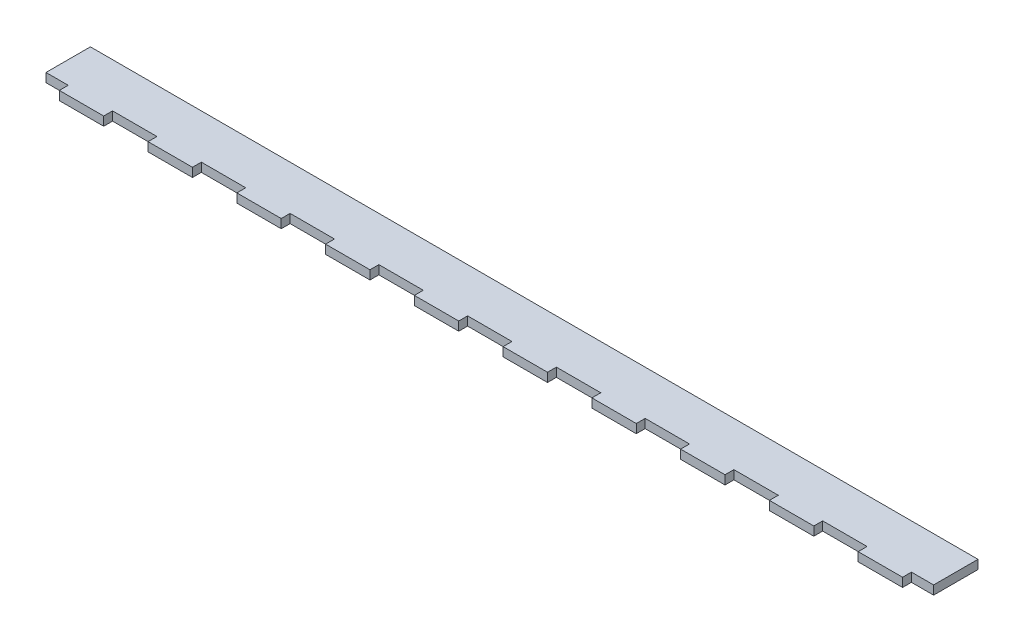
SolidWorks part; units mm, degrees
ref_plane "Front Plane" through (0, 0, 0) normal (0, 0, 1) x (1, 0, 0)
ref_plane "Top Plane" through (0, 0, 0) normal (0, 1, 0) x (1, 0, 0)
ref_plane "Right Plane" through (0, 0, 0) normal (1, 0, 0) x (0, 0, -1)
sketch "Sketch1" plane through (0, 0, 0) normal (0, 1, 0) x (1, 0, 0)
  line L0 (-190.5, -12.7) -> (-165.1, -12.7)
  line L1 (-254, 12.7) -> (254, 12.7)
  line L2 (-254, 12.7) -> (-254, -12.7)
  line L3 (-254, -12.7) -> (254, -12.7)
  line L4 (254, 12.7) -> (254, -12.7)
  line L5 (-254, 12.7) -> (254, -12.7) construction
  line L6 (-254, -12.7) -> (254, 12.7) construction
  line L7 (-241.3, -12.7) -> (-215.9, -12.7)
  line L8 (-241.3, -12.7) -> (-241.3, -17.78)
  line L9 (-241.3, -17.78) -> (-215.9, -17.78)
  line L10 (-215.9, -12.7) -> (-215.9, -17.78)
  line L11 (-190.5, -12.7) -> (-190.5, -17.78)
  line L12 (-190.5, -17.78) -> (-165.1, -17.78)
  line L13 (-165.1, -12.7) -> (-165.1, -17.78)
  line L14 (-139.7, -12.7) -> (-114.3, -12.7)
  line L15 (-139.7, -12.7) -> (-139.7, -17.78)
  line L16 (-139.7, -17.78) -> (-114.3, -17.78)
  line L17 (-114.3, -12.7) -> (-114.3, -17.78)
  line L18 (-88.9, -12.7) -> (-63.5, -12.7)
  line L19 (-88.9, -12.7) -> (-88.9, -17.78)
  line L20 (-88.9, -17.78) -> (-63.5, -17.78)
  line L21 (-63.5, -12.7) -> (-63.5, -17.78)
  line L22 (-38.1, -12.7) -> (-12.7, -12.7)
  line L23 (-38.1, -12.7) -> (-38.1, -17.78)
  line L24 (-38.1, -17.78) -> (-12.7, -17.78)
  line L25 (-12.7, -12.7) -> (-12.7, -17.78)
  line L26 (12.7, -12.7) -> (38.1, -12.7)
  line L27 (12.7, -12.7) -> (12.7, -17.78)
  line L28 (12.7, -17.78) -> (38.1, -17.78)
  line L29 (38.1, -12.7) -> (38.1, -17.78)
  line L30 (63.5, -12.7) -> (88.9, -12.7)
  line L31 (63.5, -12.7) -> (63.5, -17.78)
  line L32 (63.5, -17.78) -> (88.9, -17.78)
  line L33 (88.9, -12.7) -> (88.9, -17.78)
  line L34 (114.3, -12.7) -> (139.7, -12.7)
  line L35 (114.3, -12.7) -> (114.3, -17.78)
  line L36 (114.3, -17.78) -> (139.7, -17.78)
  line L37 (139.7, -12.7) -> (139.7, -17.78)
  line L38 (165.1, -12.7) -> (190.5, -12.7)
  line L39 (165.1, -12.7) -> (165.1, -17.78)
  line L40 (165.1, -17.78) -> (190.5, -17.78)
  line L41 (190.5, -12.7) -> (190.5, -17.78)
  line L42 (215.9, -12.7) -> (241.3, -12.7)
  line L43 (215.9, -12.7) -> (215.9, -17.78)
  line L44 (215.9, -17.78) -> (241.3, -17.78)
  line L45 (241.3, -12.7) -> (241.3, -17.78)
  point P0 (0, 0)
  dimension "D1" = 25.4
  dimension "D2" = 508
  dimension "D3" = 5.08
  dimension "D4" = 25.4
  dimension "D5" = 241.3
  dimension "D7" = 50.8
  dimension "D6" = 10
extrude "Boss-Extrude1" add sketch "Sketch1" along normal blind 5.08 contours L4 L1 L2 L3 L0 | L10 L3 L8 L9 | L17 L3 L15 L16 | L25 L3 L23 L24 | L29 L3 L27 L28 | L20 L21 L18 L19 | L32 L33 L30 L31 | L36 L37 L34 L35 | L40 L41 L38 L39 | L44 L45 L42 L43
